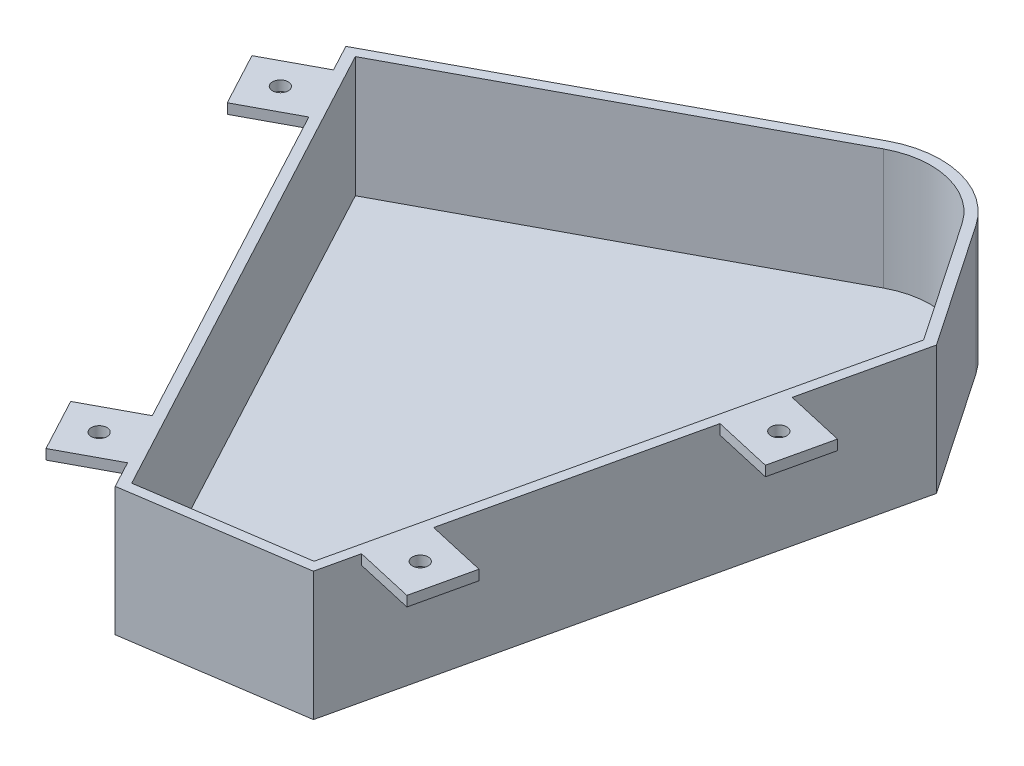
SolidWorks part; units mm, degrees
ref_plane "Front Plane" through (0, 0, 0) normal (0, 0, 1) x (1, 0, 0)
ref_plane "Top Plane" through (0, 0, 0) normal (0, 1, 0) x (1, 0, 0)
ref_plane "Right Plane" through (0, 0, 0) normal (1, 0, 0) x (0, 0, -1)
sketch "Sketch1" plane through (0, 0, 0) normal (0, 1, 0) x (1, 0, 0)
  line L0 (108.6945, 58.1876) -> (0, 0)
  line L3 (131.6337, -144.6761) -> (167.3968, 12.2534)
  line L4 (167.3968, 12.2534) -> (141.6887, 50.0735)
  line L6 (81.4356, -152.1218) -> (0, 0)
  line L7 (81.4356, -152.1218) -> (131.6337, -144.6761)
  arc A0 (141.6887, 50.0735) -> (108.6945, 58.1876) centre (120.6823, 35.7944) ccw
  dimension "D5" = 172.548
  dimension "D6" = 90
extrude "Boss-Extrude1" add sketch "Sketch1" along normal blind 2.54
sketch "Sketch2" plane through (0, 2.54, 0) normal (0, 1, 0) x (1, 0, 0)
  line L11 (81.4356, -152.1218) -> (0, 0)
  line L12 (0, 0) -> (108.6945, 58.1876)
  line L13 (141.6887, 50.0735) -> (167.3968, 12.2534)
  line L14 (167.3968, 12.2534) -> (131.6337, -144.6761)
  line L16 (79.6911, -155.5903) -> (-4.2976, 1.3007)
  line L17 (-4.2976, 1.3007) -> (107.196, 60.9867)
  line L18 (144.3145, 51.8584) -> (170.7995, 12.8953)
  line L19 (170.7995, 12.8953) -> (134.2469, -147.4982)
  line L20 (131.6337, -144.6761) -> (81.4356, -152.1218) construction
  line L21 (134.2469, -147.4982) -> (79.6911, -155.5903) construction
  line L24 (81.4356, -152.1218) -> (131.6337, -144.6761)
  line L25 (134.2469, -147.4982) -> (79.6911, -155.5903)
  arc A0 (108.6945, 58.1876) -> (141.6887, 50.0735) centre (120.6823, 35.7944) cw
  arc A1 (107.196, 60.9867) -> (144.3145, 51.8584) centre (120.6823, 35.7944) cw
  point P14 (0, 0)
  point P15 (-12.4923, -8.5992)
  point P16 (81.4356, -152.1218)
  point P17 (70.5427, -160.4756)
  point P18 (0, 0)
  dimension "D1" = 3.175
extrude "Boss-Extrude5" add sketch "Sketch2" along normal blind 38.1 and the other way up to surface (2.54 mm away) other way up to face at (105.4009, 0, 28.3257)
sketch "Sketch6" plane through (159.5733, 0, 36.3657) normal (0.975, 0, 0.2222) x (0.2222, 0, -0.975)
  line L0 (-113.9819, 40.64) -> (50.524, 40.64) construction
  line L1 (-6.626, 40.64) -> (12.424, 40.64)
  line L2 (-6.626, 40.64) -> (-6.626, 37.465)
  line L3 (-6.626, 37.465) -> (12.424, 37.465)
  line L4 (12.424, 40.64) -> (12.424, 37.465)
  line L5 (50.524, 40.64) -> (50.524, 0) construction
  line L6 (-82.2319, 40.64) -> (-101.2819, 40.64)
  line L7 (-82.2319, 40.64) -> (-82.2319, 37.465)
  line L8 (-82.2319, 37.465) -> (-101.2819, 37.465)
  line L9 (-101.2819, 40.64) -> (-101.2819, 37.465)
  line L10 (-113.9819, 40.64) -> (-113.9819, 0) construction
  dimension "D1" = 3.175
  dimension "D2" = 38.1
  dimension "D3" = 19.05
  dimension "D4" = 19.05
  dimension "D5" = 3.175
  dimension "D6" = 12.7
extrude "Boss-Extrude6" add sketch "Sketch6" along normal blind 19.05
sketch "Sketch7" plane through (-2.7991, 0, 1.4985) normal (-0.8816, 0, 0.472) x (0.472, 0, 0.8816)
  line L0 (-3.175, 40.64) -> (174.7825, 40.64) construction
  line L1 (6.35, 40.64) -> (25.4, 40.64)
  line L2 (6.35, 40.64) -> (6.35, 37.465)
  line L3 (6.35, 37.465) -> (25.4, 37.465)
  line L4 (25.4, 40.64) -> (25.4, 37.465)
  line L5 (-3.175, 40.64) -> (-3.175, 0) construction
  line L6 (165.2575, 40.64) -> (146.2075, 40.64)
  line L7 (165.2575, 40.64) -> (165.2575, 37.465)
  line L8 (165.2575, 37.465) -> (146.2075, 37.465)
  line L9 (146.2075, 40.64) -> (146.2075, 37.465)
  line L10 (174.7825, 40.64) -> (174.7825, 0) construction
  dimension "D1" = 19.05
  dimension "D2" = 19.05
  dimension "D3" = 3.175
  dimension "D4" = 3.175
  dimension "D5" = 9.525
  dimension "D6" = 9.525
extrude "Boss-Extrude7" add sketch "Sketch7" along normal blind 19.05
sketch "Sketch8" plane through (0, 37.465, 0) normal (0, -1, 0) x (-1, 0, 0)
  line L0 (8.1996, -11.5922) -> (-0.7912, -28.387) construction
  line L1 (16.5971, -16.0876) -> (-0.1978, -7.0968) construction
  line L2 (7.6062, -32.8825) -> (-9.1886, -23.8916) construction
  line L4 (-49.41, -139.3888) -> (-66.2049, -130.398) construction
  line L5 (-57.8074, -134.8934) -> (-66.7982, -151.6883) construction
  line L6 (-58.4008, -156.1837) -> (-75.1957, -147.1929) construction
  line L8 (-155.6426, -139.3485) -> (-137.0688, -135.1157) construction
  line L9 (-146.3557, -137.2321) -> (-150.5885, -118.6583) construction
  line L10 (-159.8754, -120.7747) -> (-141.3016, -116.5419) construction
  line L12 (-176.6748, -47.0589) -> (-158.101, -42.8261) construction
  line L13 (-167.3879, -44.9425) -> (-171.6207, -26.3687) construction
  line L14 (-180.9076, -28.4851) -> (-162.3338, -24.2523) construction
  circle A0 centre (3.7042, -19.9896) radius 2.4892
  circle A1 centre (-62.3028, -143.2909) radius 2.4892
  circle A2 centre (-148.4721, -127.9452) radius 2.4892
  circle A3 centre (-169.5043, -35.6556) radius 2.4892
  dimension "D1" = 4.9784
extrude "Cut-Extrude2" cut sketch "Sketch8" against normal up to next
